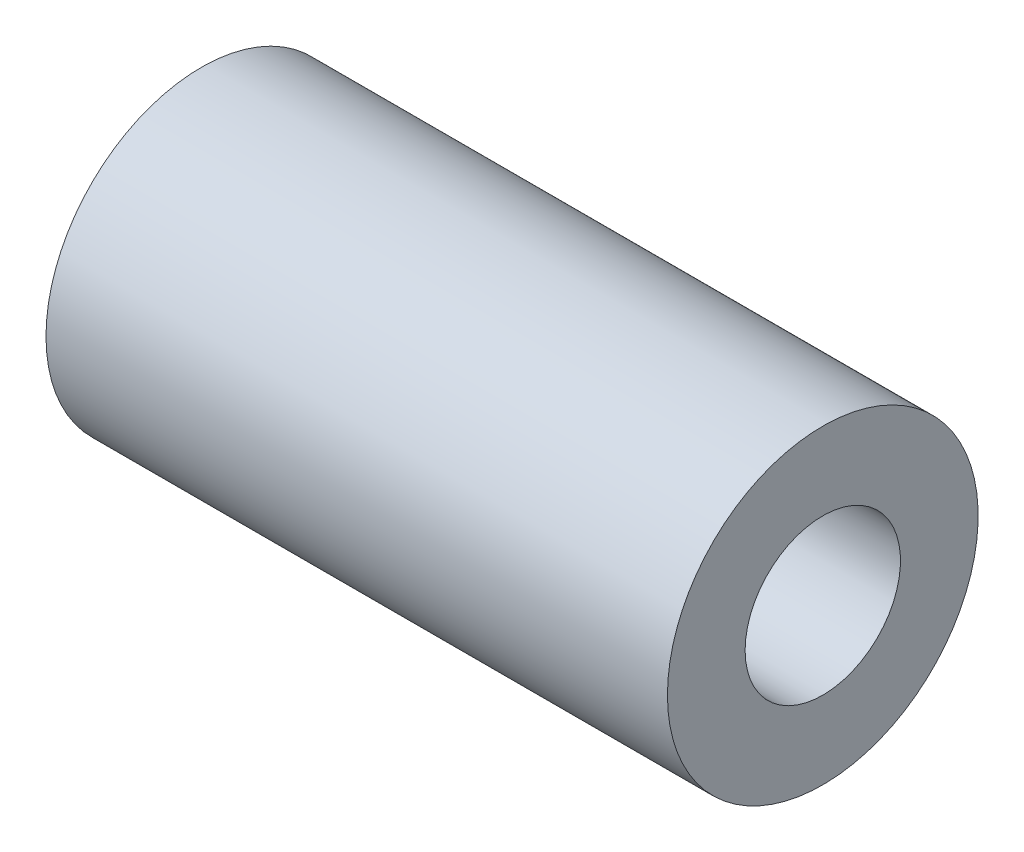
SolidWorks part; units mm, degrees
material "POM Acetal Copolymer"
ref_plane "Front Plane" through (0, 0, 0) normal (0, 0, 1) x (1, 0, 0)
ref_plane "Top Plane" through (0, 0, 0) normal (0, 1, 0) x (1, 0, 0)
ref_plane "Right Plane" through (0, 0, 0) normal (1, 0, 0) x (0, 0, -1)
sketch "Sketch1" plane through (0, 0, 0) normal (0, 0, 1) x (1, 0, 0)
  line L0 (-5, 0) -> (15.7129, 0) construction
  line L1 (-5, 0) -> (5, 0)
  line L2 (-5, 0) -> (-5, 2.5)
  line L3 (-5, 2.5) -> (5, 2.5)
  line L4 (5, 0) -> (5, 2.5)
  dimension "D1" = 10
  dimension "D2" = 5
revolve "Revolve1" add sketch "Sketch1" angle 360 about L0
hole_wizard "Trou taraudé M31" positions "Sketch3" profile "Sketch2" tap size "M3" standard "Iso" end condition through all
sketch "Sketch3" plane through (-5, 0, 0) normal (-1, 0, 0) x (0, 0, 1)
  point P0 (0, 0)
sketch "Sketch2" plane through (-5, 0, 0) normal (0, 1, 0) x (0, 0, 1)
  line L0 (0, 0) -> (0, 10)
  line L1 (0, 10) -> (1.25, 10)
  line L2 (1.25, 10) -> (1.25, 0)
  line L5 (1.25, 0) -> (0, 0)
  line L11 (0, -6.35) -> (0, 107.95) construction
  dimension "Diamètre du trou pour taraudage jusqu'au prochain" = 2.5
  dimension "Profondeur du trou pour taraudage jusqu'au prochain" = 10
cosmetic thread "Filetage de perçage1" parameters "D2"=3
